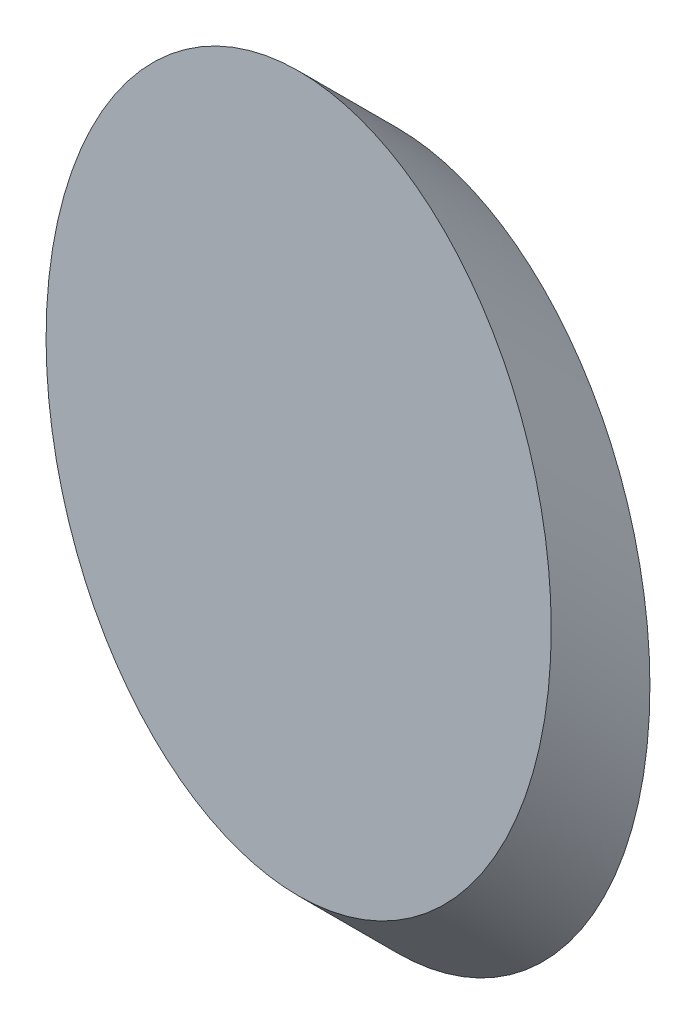
SolidWorks part; units mm, degrees
ref_plane "前视基准面" through (0, 0, 0) normal (0, 0, 1) x (1, 0, 0)
ref_plane "上视基准面" through (0, 0, 0) normal (0, 1, 0) x (1, 0, 0)
ref_plane "右视基准面" through (0, 0, 0) normal (1, 0, 0) x (0, 0, -1)
sketch "草图1" plane through (0, 0, 0) normal (0, 0, 1) x (1, 0, 0)
  ellipse E0 centre (54.3924, 35.7889) end of major axis (54.3924, 81.0489) minor radius 32
  dimension "D1" = 64
  dimension "D2" = 90.52
sketch3d "3D草图2"
  line L0 (55.1123, 81.0374, 0) -> (55.1123, 81.0374, -2.7888)
  line L3 (55.1123, 81.0374, 0) -> (55.1123, 76.0858, -4.9516)
  line L4 (55.1123, 81.0374, 0) -> (55.1123, 28.9476, 0)
  spline S2 degree 3 poles (54.3924, 81.0489, 0) (-9.6076, 81.0489, 0) (-9.6076, -9.4711, 0) (54.3924, -9.4711, 0) (118.3924, -9.4711, 0) (118.3924, 81.0489, 0) (54.3924, 81.0489, 0) (-9.6076, 81.0489, 0) (-9.6076, -9.4711, 0) knots -0.5 0 0 0 0.5 0.5 0.5 1 1 1 1.5 1.5 1.5 weights 1 0.333333 0.333333 1 0.333333 0.333333 1 0.333333 0.333333 only from (54.3924, 81.0489, 0) to (54.3924, 81.0489, 0) construction
  dimension "D1" = 45
extrude "凸台-拉伸2" add sketch "草图1" along direction (0, -0.7071, -0.7071) on the side of the normal blind 17.68
